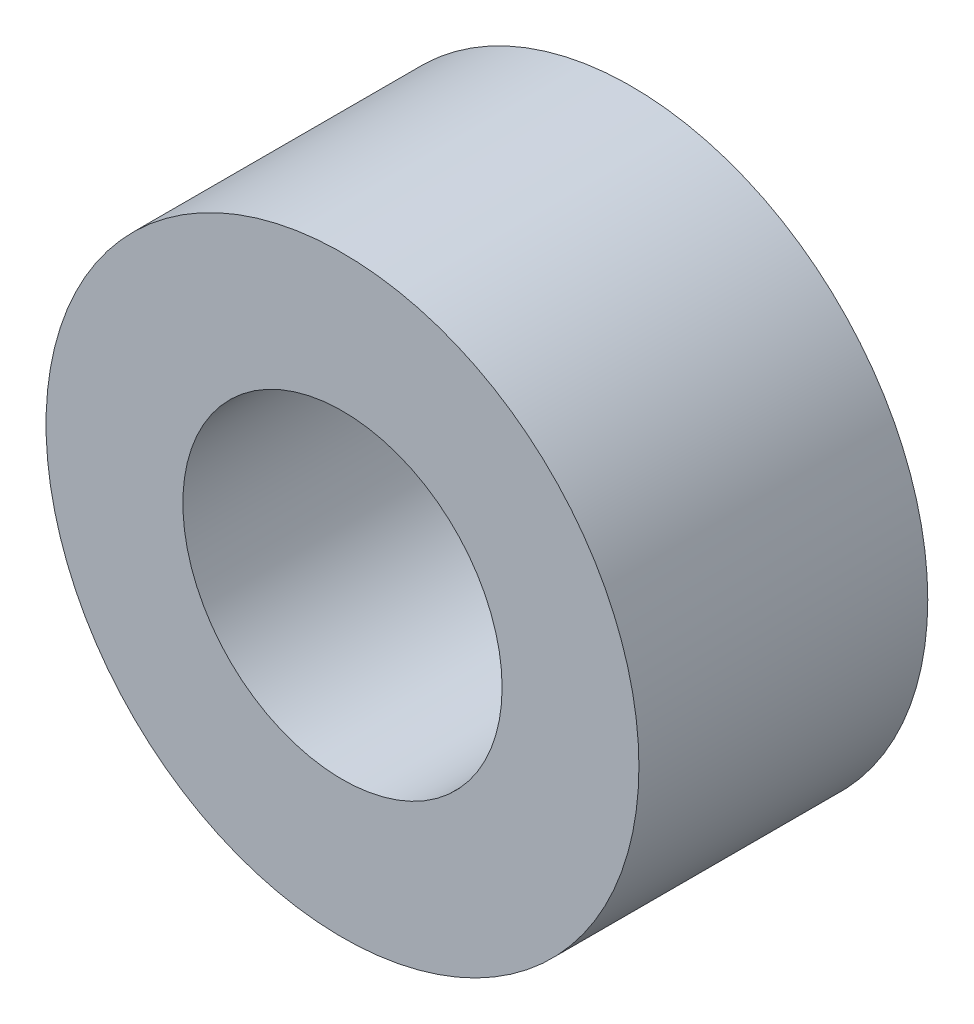
SolidWorks part; units mm, degrees
material "AISI 1045 Steel, cold drawn"
ref_plane "Front Plane" through (0, 0, 0) normal (0, 0, 1) x (1, 0, 0)
ref_plane "Top Plane" through (0, 0, 0) normal (0, 1, 0) x (1, 0, 0)
ref_plane "Right Plane" through (0, 0, 0) normal (1, 0, 0) x (0, 0, -1)
sketch "Sketch1" plane through (0, 0, 0) normal (0, 0, 1) x (1, 0, 0)
  circle A0 centre (0, 0) radius 10.5
  circle A1 centre (0, 0) radius 19.5
  dimension "D1" = 21
  dimension "D2" = 39
extrude "Boss-Extrude1" add sketch "Sketch1" along normal blind 19
